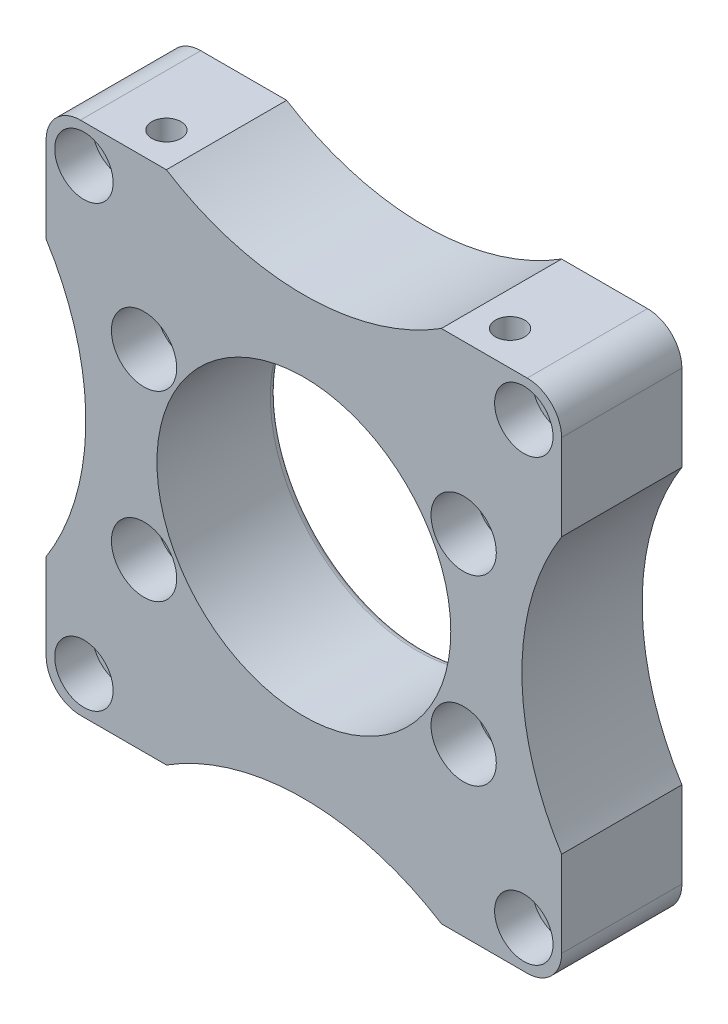
SolidWorks part; units mm, degrees
ref_plane "Plan de face" through (0, 0, 0) normal (0, 0, 1) x (1, 0, 0)
ref_plane "Plan de dessus" through (0, 0, 0) normal (0, 1, 0) x (1, 0, 0)
ref_plane "Plan de droite" through (0, 0, 0) normal (1, 0, 0) x (0, 0, -1)
sketch "Esquisse2" plane through (0, 0, 0) normal (0, 0, 1) x (1, 0, 0)
  line L1 (-150, 150) -> (0, 150)
  line L2 (-150, 150) -> (-150, 0)
  line L3 (-150, 0) -> (0, 0)
  line L4 (0, 150) -> (0, 0)
  line L5 (-150, 150) -> (0, 0) construction
  line L6 (-150, 0) -> (0, 150) construction
  point P0 (-75, 75)
  dimension "D1" = 150
  dimension "D2" = 150
extrude "Boss.-Extru.1" add sketch "Esquisse2" along normal blind 35
sketch "Esquisse3" plane through (0, 0, 35) normal (0, 0, 1) x (1, 0, 0)
  line L0 (-150, 0) -> (0, 0) construction
  line L1 (0, 0) -> (0, 150) construction
  circle A0 centre (-75, 75) radius 42.75
  point P4 (0, 75)
  dimension "D1" = 85.5
  dimension "D2" = 75
  dimension "D3" = 75
extrude "Enlèv. mat.-Extru.2" cut sketch "Esquisse3" against normal blind 40
sketch "Esquisse5" plane through (0, 0, 35) normal (0, 0, 1) x (1, 0, 0)
  line L0 (0, 150) -> (-150, 150) construction
  line L1 (-150, 0) -> (0, 0) construction
  line L2 (-150, 150) -> (-150, 0) construction
  line L3 (0, 0) -> (0, 150) construction
  circle A0 centre (-28.5, 101.5) radius 6
  circle A1 centre (-28.5, 48.5) radius 6
  circle A2 centre (-121.5, 48.5) radius 6
  circle A3 centre (-121.5, 101.5) radius 6
  dimension "D1" = 12
  dimension "D2" = 12
  dimension "D3" = 12
  dimension "D4" = 12
  dimension "D5" = 48.5
  dimension "D6" = 48.5
  dimension "D7" = 48.5
  dimension "D8" = 48.5
  dimension "D9" = 28.5
  dimension "D10" = 28.5
  dimension "D11" = 28.5
  dimension "D12" = 28.5
extrude "Enlèv. mat.-Extru.3" cut sketch "Esquisse5" against normal blind 40
sketch "Esquisse6" plane through (0, 0, 35) normal (0, 0, 1) x (1, 0, 0)
  circle A0 centre (-28.5, 101.5) radius 9.5
  circle A1 centre (-28.5, 48.5) radius 9.5
  circle A2 centre (-121.5, 48.5) radius 9.5
  circle A3 centre (-121.5, 101.5) radius 9.5
  dimension "D1" = 19
  dimension "D2" = 19
  dimension "D3" = 19
  dimension "D4" = 19
extrude "Enlèv. mat.-Extru.4" cut sketch "Esquisse6" against normal blind 13
sketch "Esquisse7" plane through (0, 0, 35) normal (0, 0, 1) x (1, 0, 0)
  line L0 (0, 150) -> (-150, 150) construction
  line L1 (0, 0) -> (0, 150) construction
  line L2 (-150, 0) -> (0, 0) construction
  line L3 (-150, 150) -> (-150, 0) construction
  circle A0 centre (-11, 139) radius 5.25
  circle A1 centre (-11, 11) radius 5.25
  circle A2 centre (-139, 11) radius 5.25
  circle A3 centre (-139, 139) radius 5.25
  dimension "D1" = 10.5
  dimension "D2" = 10.5
  dimension "D3" = 10.5
  dimension "D4" = 10.5
  dimension "D5" = 11
  dimension "D6" = 11
  dimension "D7" = 11
  dimension "D8" = 11
  dimension "D9" = 11
  dimension "D10" = 11
  dimension "D11" = 11
  dimension "D12" = 11
extrude "Enlèv. mat.-Extru.5" cut sketch "Esquisse7" against normal blind 40
sketch "Esquisse8" plane through (0, 0, 35) normal (0, 0, 1) x (1, 0, 0)
  circle A0 centre (-11, 139) radius 8.5
  circle A1 centre (-11, 11) radius 8.5
  circle A2 centre (-139, 11) radius 8.5
  circle A3 centre (-139, 139) radius 8.5
  dimension "D1" = 17
  dimension "D2" = 17
  dimension "D3" = 17
  dimension "D4" = 17
extrude "Enlèv. mat.-Extru.6" cut sketch "Esquisse8" against normal blind 11
sketch "Esquisse9" plane through (0, 150, 0) normal (0, 1, 0) x (1, 0, 0)
  line L0 (0, -35) -> (0, 0) construction
  line L1 (0, -35) -> (-150, -35) construction
  line L2 (-150, -35) -> (-150, 0) construction
  circle A0 centre (-25, -25) radius 4.25
  circle A1 centre (-125, -25) radius 4.25
  dimension "D1" = 8.5
  dimension "D2" = 8.5
  dimension "D3" = 25
  dimension "D4" = 10
  dimension "D5" = 10
  dimension "D6" = 25
extrude "Enlèv. mat.-Extru.7" cut sketch "Esquisse9" against normal blind 25
sketch "Esquisse15" plane through (0, 150, 0) normal (0, 1, 0) x (1, 0, 0)
  circle A0 centre (-125, -25) radius 5
  dimension "D1" = 10
curve "Hélice/Spirale2" pitch 1.5 height 25 turns 16.6667
sketch "Esquisse17" plane through (0, 150, 0) normal (0, 1, 0) x (1, 0, 0)
  circle A0 centre (-25, -25) radius 5
  dimension "D1" = 10
curve "Hélice/Spirale3" pitch 1.5 height 25 turns 16.6667
sketch "Esquisse19" plane through (0, 0, 35) normal (0, 0, 1) x (1, 0, 0)
  line L0 (0, 0) -> (0, 150) construction
  line L1 (0, 150) -> (-150, 150) construction
  line L2 (-150, 0) -> (0, 0) construction
  arc A0 (0, 115) -> (0, 35) centre (63.4429, 75) ccw
  dimension "D1" = 35
  dimension "D2" = 35
extrude "Enlèv. mat.-Extru.8" cut sketch "Esquisse19" against normal through all and the other way through all contours A0
sketch "Esquisse22" plane through (0, 0, 35) normal (0, 0, 1) x (1, 0, 0)
  line L0 (-150, 0) -> (0, 0) construction
  line L1 (0, 0) -> (0, 35) construction
  line L2 (-150, 150) -> (-150, 0) construction
  arc A0 (-115, 0) -> (-35, 0) centre (-75, -63.4429) cw
  dimension "D1" = 35
  dimension "D2" = 35
extrude "Enlèv. mat.-Extru.12" cut sketch "Esquisse22" against normal through all and the other way through all flip side to cut
sketch "Esquisse27" plane through (0, 0, 35) normal (0, 0, 1) x (1, 0, 0)
  line L0 (-150, 150) -> (-150, 0) construction
  line L1 (0, 150) -> (-150, 150) construction
  line L2 (-150, 0) -> (-115, 0) construction
  arc A0 (-150, 115) -> (-150, 35) centre (-213.4429, 75) cw
  dimension "D1" = 35
  dimension "D2" = 35
extrude "Enlèv. mat.-Extru.13" cut sketch "Esquisse27" against normal through all and the other way through all flip side to cut
sketch "Esquisse28" plane through (0, 0, 35) normal (0, 0, 1) x (1, 0, 0)
  line L0 (0, 150) -> (-150, 150) construction
  line L1 (0, 115) -> (0, 150) construction
  line L2 (-150, 150) -> (-150, 115) construction
  arc A0 (-115, 150) -> (-35, 150) centre (-75, 213.4429) ccw
  dimension "D1" = 35
  dimension "D2" = 35
extrude "Enlèv. mat.-Extru.14" cut sketch "Esquisse28" against normal through all and the other way through all
fillet "Congé1" radius 10 1 edges at (0, 150, 17.5)
fillet "Congé2" radius 10 1 edges at (-150, 150, 17.5)
fillet "Congé3" radius 10 1 edges at (-150, 0, 17.5)
fillet "Congé4" radius 10 1 edges at (0, 0, 17.5)
fillet "Congé5" radius 2 1 edges at (-32.25, 75, 0)
